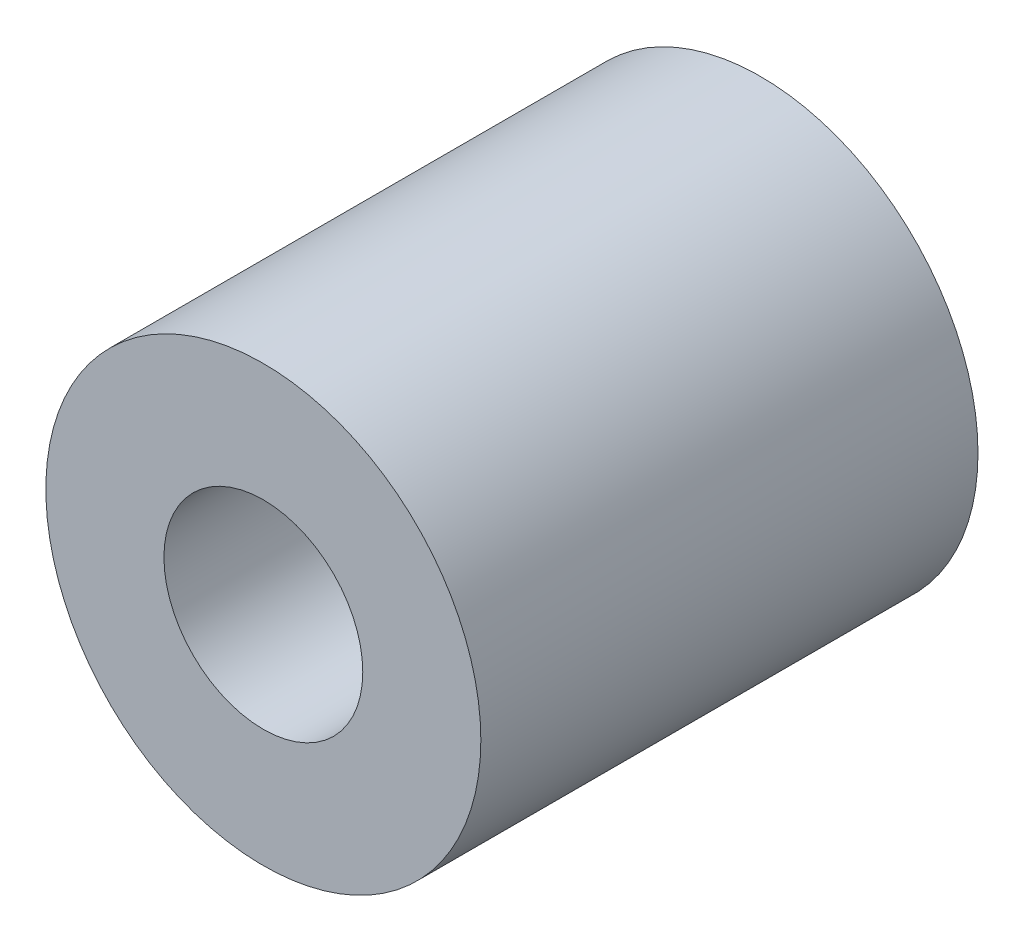
SolidWorks part; units mm, degrees
material "尼龙 101"
ref_plane "前视基准面" through (0, 0, 0) normal (0, 0, 1) x (1, 0, 0)
ref_plane "上视基准面" through (0, 0, 0) normal (0, 1, 0) x (1, 0, 0)
ref_plane "右视基准面" through (0, 0, 0) normal (1, 0, 0) x (0, 0, -1)
sketch "草图1" plane through (0, 0, 0) normal (0, 0, 1) x (1, 0, 0)
  circle A0 centre (0, 0) radius 3.5
  circle A1 centre (0, 0) radius 1.6
  dimension "D1" = 7
  dimension "D2" = 3.2
extrude "凸台-拉伸1" add sketch "草图1" along normal mid plane 8
